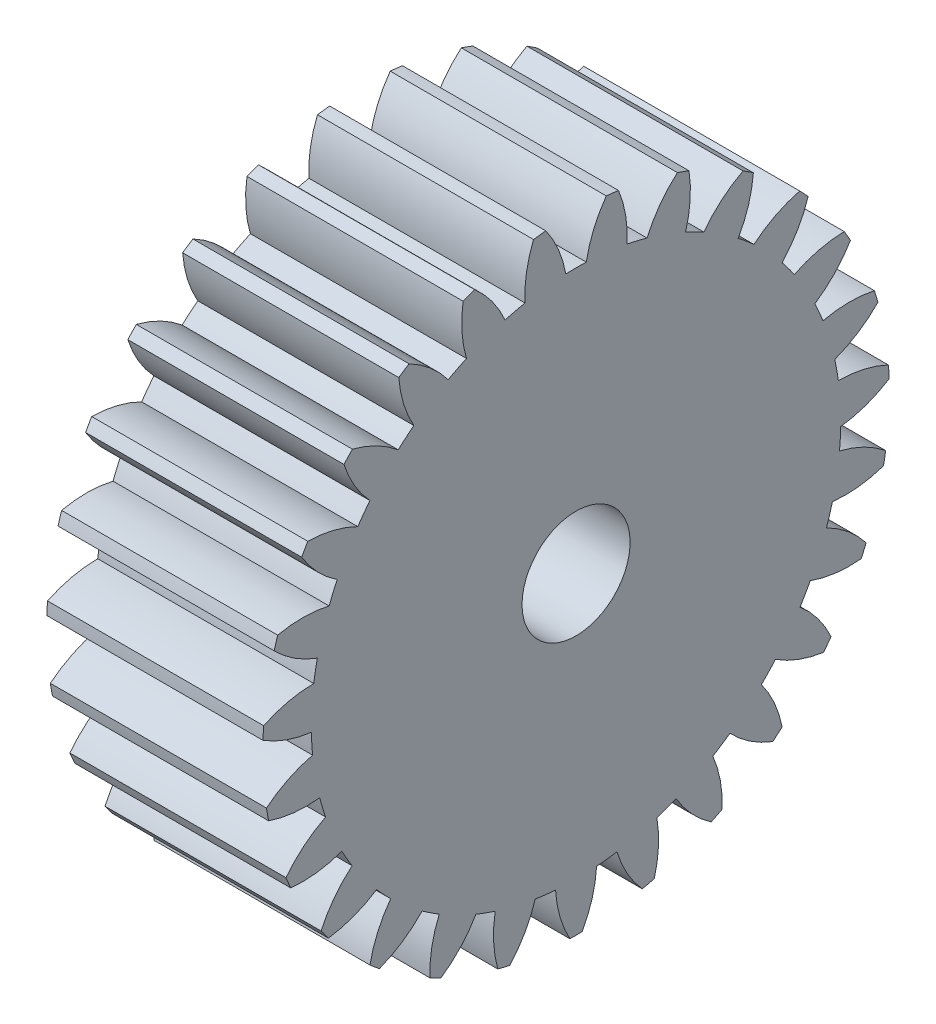
SolidWorks part; units mm, degrees
ref_plane "Plane1" through (0, 0, 0) normal (0, 0, 1) x (1, 0, 0)
ref_plane "Plane2" through (0, 0, 0) normal (0, 1, 0) x (1, 0, 0)
ref_plane "Plane3" through (0, 0, 0) normal (1, 0, 0) x (0, 0, -1)
other "Configuration Table"
sketch "HoldingSke" plane through (0, 0, 0) normal (0, 1, 0) x (1, 0, 0)
  line L0 (0, 0) -> (0.891, -0.454)
  line L1 (-15, 0) -> (100, 0) construction
  line L2 (0, 0) -> (-2.1039, 2.3779)
  line L3 (0, 0) -> (-11.863, 4.5341)
  line L4 (0, 0) -> (7.6947, 3.9207)
  line L5 (0, 0) -> (-46.8476, -17.4728)
  line L6 (0, 0) -> (-8.2896, -5.593)
  line L7 (-2.1039, 2.3779) -> (8.6586, 51.2059)
  line L8 (-76.2, 54.61) -> (-75.3, 54.61)
  line L9 (-71.009, 38.7566) -> (-53.1078, 45.2721)
  line L10 (-76.2, 71.12) -> (104.1128, 71.12)
  line L11 (0, 0) -> (-10, 0)
  line L12 (-76.2, 101.6) -> (-76.162, 101.6)
  line L13 (24.9733, 27.94) -> (52.9518, 28.4284)
  line L14 (24.9733, 27.94) -> (24.9743, 27.94)
  line L15 (24.9733, 27.94) -> (100.4006, 29.5858)
  line L16 (-63.627, -1) -> (-12.827, -1)
  circle A0 centre (0, 0) radius 2.5
  circle A1 centre (0, 0) radius 12.249
  circle A2 centre (0, 0) radius 37.5
  circle A3 centre (0, 0) radius 2.5
  dimension "MHD" = 24.498
  dimension "Hub_dia" = 75
  dimension "Bore" = 5
  dimension "MBD" = 5
  dimension "Num_teeth" = 27
  dimension "Pitch" = 1
  dimension "Overall_len" = 50
  dimension "Show_teeth" = 27
  dimension "Thickness" = 10
  dimension "OAL" = 50.0001
  dimension "T_dim" = 0.9
  dimension "Ap" = 20
  dimension "H" = 19.05
  dimension "Pitch_radius" = 180.3128
  dimension "Width" = 10
  dimension "Backlash" = 0.038
  dimension "Addendum_fac" = 1
  dimension "Dedendum_fac" = 1.25
  dimension "Clearance_fac" = 0.25
  dimension "Dedendum_add" = 0.001
  dimension "Module" = 1
sketch "BasProSke" plane through (0, 0, 0) normal (0, 1, 0) x (1, 0, 0)
  line L0 (-10, 0) -> (60, 0) construction
  line L1 (0, 0) -> (0, 14.5)
  line L2 (0, 0) -> (10, 0)
  line L3 (10, 0) -> (10, 14.5)
  line L4 (10, 14.5) -> (0, 14.5)
  dimension "Thickness" = 10
  dimension "Diameter" = 29
revolve "Base-Revolve" add sketch "BasProSke" angle 360 about L0
sketch "TooCutSke" plane through (0, 0, 0) normal (1, 0, 0) x (0, 0, -1)
  line L1 (0, 0) -> (0, 107) construction
  line L2 (0, 0) -> (-0.8514, 13.4731) construction
  line L3 (0, 0) -> (-3.1301, 26.7794) construction
  line L4 (-0.8514, 13.4731) -> (-1.565, 13.3897) construction
  arc A0 (0.4741, 12.2398) -> (-0.4741, 12.2398) centre (0, 0) ccw
  arc A1 (1.4167, 14.4561) -> (-1.4167, 14.4561) centre (0, 0) ccw
  circle A2 centre (0, 0) radius 13.5 construction
  circle A3 centre (0, 0) radius 12.6859 construction
  arc A4 (-0.4741, 12.2398) -> (-1.4167, 14.4561) centre (-5.7895, 11.2877) ccw
  arc A5 (1.4167, 14.4561) -> (0.4741, 12.2398) centre (5.7895, 11.2877) ccw
  dimension "Root_dia" = 24.498
  dimension "Overcut_dia" = 29.0508
  dimension "Pitch_dia" = 27
  dimension "Base_dia" = 25.3717
  dimension "Flank_rad" = 5.4
  dimension "Half_ang" = 6.667
  dimension "Half_CT" = 0.7185
extrude "ToothCut" cut sketch "TooCutSke" along normal through all
fillet "Breaks" [suppressed] radius 0.02
fillet "RootFillets" [suppressed] radius 0.251
pattern_circular "TeethCuts" count 27 every 13.333 about axis through (-10, 0, 0) along (1, 0, 0) of "ToothCut", "RootFillets", "Breaks"
sketch "HubNeaOneSke" plane through (0, 0, 0) normal (-1, 0, 0) x (0, 0, 1)
  circle A0 centre (0, 0) radius 12.249
  dimension "Diameter" = 24.498
extrude "HubNearOne" [suppressed] add sketch "HubNeaOneSke" along normal blind 40.0001
sketch "HubNeaBotSke" plane through (0, 0, 0) normal (-1, 0, 0) x (0, 0, 1)
  circle A0 centre (0, 0) radius 12.249
  dimension "Diameter" = 24.498
extrude "HubNearBoth" [suppressed] add sketch "HubNeaBotSke" along normal blind 20
ref_plane "FarPln" through (10, 0, 0) normal (1, 0, 0) x (0, 0, -1)
sketch "HubFarSke" plane through (10, 0, 0) normal (1, 0, 0) x (0, 0, -1)
  circle A0 centre (0, 0) radius 12.249
  dimension "Diameter" = 24.498
extrude "HubFar" [suppressed] add sketch "HubFarSke" along normal blind 20
sketch "BorSke" plane through (0, 0, 0) normal (1, 0, 0) x (0, 0, -1)
  circle A0 centre (0, 0) radius 2.5
  dimension "Diameter" = 5
extrude "Bore" cut sketch "BorSke" along normal mid plane 100.0001
sketch "KeySke" plane through (0, 0, 0) normal (1, 0, 0) x (0, 0, -1)
  line L0 (-1, 0) -> (-1, 3.4)
  line L1 (-1, 3.4) -> (1, 3.4)
  line L2 (1, 3.4) -> (1, 0)
  line L3 (0, 0) -> (0, 34) construction
  line L4 (-1, 0) -> (1, 0)
  dimension "Offset" = 3.4
  dimension "Width" = 2
extrude "Keyway" [suppressed] cut sketch "KeySke" along normal mid plane 100.0001
pattern_circular "Keyway2" [suppressed] count 2 every 90 about axis through (-10, 0, 0) along (1, 0, 0)
equation "' \"Module@HoldingSke\" = 6.35"
equation "' \"Num_teeth@HoldingSke\" = 12"
equation "' \"Ap@HoldingSke\" =  20"
equation "' \"Ap@HoldingSke\" = 20"
equation "' \"Width@HoldingSke\" = 0.5 * 25.4"
equation "' \"Hub_dia@HoldingSke\"= 1 * 25.4"
equation "' \"Hub_dia@HoldingSke\" = 1 * 25.4"
equation "' \"Overall_len@HoldingSke\" = 1.0 * 25.4"
equation "' \"Bore@HoldingSke\" = 0.75 * 25.4"
equation "' \"T_dim@HoldingSke\" = 0.1 * 25.4"
equation "' \"Width@KeySke\" = 0.25 * 25.4"
equation "' \"Show_teeth@HoldingSke\" = 13"
equation "' \"Backlash@HoldingSke\" = 0.009 * 25.4"
equation "' \"Addendum_fac@HoldingSke\" = 1.0"
equation "' \"Dedendum_fac@HoldingSke\" = 1.25"
equation "' \"Dedendum_add@HoldingSke\" = 0.00005 * 25.4"
equation "' \"Clearance_fac@HoldingSke\" = 0.25"
equation "\"Pitch@HoldingSke\" = 1 / \"Module@HoldingSke\""
equation "\"Overcut_dia@TooCutSke\" = (\"Num_teeth@HoldingSke\" + 2 * \"Addendum_fac@HoldingSke\") / \"Pitch@HoldingSke\" + 0.002 * 25.4"
equation "\"Pitch_dia@TooCutSke\" = \"Num_teeth@HoldingSke\" / \"Pitch@HoldingSke\""
equation "\"Base_dia@TooCutSke\" = \"Num_teeth@HoldingSke\" / \"Pitch@HoldingSke\" * cos((\"Ap@HoldingSke\"  * 3.14159265 / 180))"
equation "\"Root_dia@TooCutSke\" = (\"Num_teeth@HoldingSke\" + 2) / \"Pitch@HoldingSke\" - 2 * (\"Addendum_fac@HoldingSke\" + \"Dedendum_fac@HoldingSke\") / \"Pitch@HoldingSke\" - \"Dedendum_add@HoldingSke\" * 2"
equation "\"Half_ang@TooCutSke\" = 180 / \"Num_teeth@HoldingSke\""
equation "\"Half_CT@TooCutSke\" = \"Num_teeth@HoldingSke\" / \"Pitch@HoldingSke\" * sin((3.14159265 / 2 / \"Num_teeth@HoldingSke\")) / 2 - 7 * \"Backlash@HoldingSke\" / 4"
equation "\"Flank_rad@TooCutSke\" = \"Num_teeth@HoldingSke\" / \"Pitch@HoldingSke\" / 5"
equation "\"Radius@RootFillets\" = \"Clearance_fac@HoldingSke\" / \"Pitch@HoldingSke\" + \"Dedendum_add@HoldingSke\""
equation "\"Break_rad@Breaks\" = 0.02 / \"Pitch@HoldingSke\""
equation "\"Thickness@HoldingSke\" = \"Width@HoldingSke\""
equation "\"OAL@HoldingSke\" = \"Thickness@HoldingSke\""
equation "\"MHD@HoldingSke\" = (\"Num_teeth@HoldingSke\" + 2) / \"Pitch@HoldingSke\" - 2 * (\"Addendum_fac@HoldingSke\" + \"Dedendum_fac@HoldingSke\")  / \"Pitch@HoldingSke\" - \"Dedendum_add@HoldingSke\" * 2"
equation "\"MBD@HoldingSke\" = (\"Num_teeth@HoldingSke\" + 2) / \"Pitch@HoldingSke\" - 2 * (\"Addendum_fac@HoldingSke\" + \"Dedendum_fac@HoldingSke\")  / \"Pitch@HoldingSke\" - \"Dedendum_add@HoldingSke\" * 2 - 0.002 * 25.4"
equation "\"MHD@HoldingSke\" = ((sgn( \"MHD@HoldingSke\" - \"Hub_dia@HoldingSke\" )-1)*( \"MHD@HoldingSke\" - \"Hub_dia@HoldingSke\" ))/-2+ \"Hub_dia@HoldingSke\""
equation "\"MBD@HoldingSke\" = ((sgn( \"MBD@HoldingSke\" - \"Bore@HoldingSke\" )-1)*( \"MBD@HoldingSke\" - \"Bore@HoldingSke\" ))/-2+ \"Bore@HoldingSke\""
equation "\"OAL@HoldingSke\" = ((sgn( \"OAL@HoldingSke\" - \"Overall_len@HoldingSke\" )+1)*( \"OAL@HoldingSke\" - \"Overall_len@HoldingSke\" ))/2 + \"Overall_len@HoldingSke\" + 0.000002 * 25.4"
equation "\"Num_teeth@TeethCuts\" = int( \"Show_teeth@HoldingSke\" ) + 1"
equation "\"Num_teeth@TeethCuts\" = ((sgn( \"Num_teeth@TeethCuts\" - \"Num_teeth@HoldingSke\" )-1)*( \"Num_teeth@TeethCuts\" - \"Num_teeth@HoldingSke\" ))/-2+ \"Num_teeth@HoldingSke\""
equation "\"Num_teeth@TeethCuts\" = ((sgn( \"Num_teeth@TeethCuts\" - 2.0)+1)*( \"Num_teeth@TeethCuts\" - 2.0))/2 +2.0"
equation "\"Angle@TeethCuts\" = 360.0 / \"Num_teeth@HoldingSke\""
equation "\"Diameter@BasProSke\" = (\"Num_teeth@HoldingSke\" + 2 * \"Addendum_fac@HoldingSke\") / \"Pitch@HoldingSke\""
equation "\"Thickness@BasProSke\"  = \"Thickness@HoldingSke\""
equation "' \"Fillet_rad@BasProSke\" =  \"Thickness@HoldingSke\" * 0.05"
equation "' \"Fillet_rad@BasProSke\" = \"Thickness@HoldingSke\" * 0.05"
equation "\"MHD@HoldingSke\" = ((sgn( \"MHD@HoldingSke\" - \"Root_dia@TooCutSke\" )-1)*( \"MHD@HoldingSke\" - \"Root_dia@TooCutSke\" ))/-2+ \"Root_dia@TooCutSke\""
equation "\"Diameter@HubNeaOneSke\" = \"MHD@HoldingSke\""
equation "\"Length@HubNearOne\" = \"OAL@HoldingSke\" - \"Thickness@BasProSke\""
equation "\"Diameter@HubNeaBotSke\" = \"MHD@HoldingSke\""
equation "\"Length@HubNearBoth\" = ( \"OAL@HoldingSke\" - \"Thickness@BasProSke\" ) / 2.0"
equation "\"Thickness@FarPln\" = \"Thickness@BasProSke\""
equation "\"Diameter@HubFarSke\" = \"MHD@HoldingSke\""
equation "\"Length@HubFar\" = ( \"OAL@HoldingSke\" - \"Thickness@BasProSke\" ) / 2.0"
equation "\"Diameter@BorSke\" = \"MBD@HoldingSke\""
equation "\"D1@Bore\" = \"OAL@HoldingSke\" * 2.0"
equation "\"D1@Keyway\" = \"OAL@HoldingSke\" * 2.0"
equation "\"Offset@KeySke\" = \"T_dim@HoldingSke\" + \"MBD@HoldingSke\" / 2.0"
